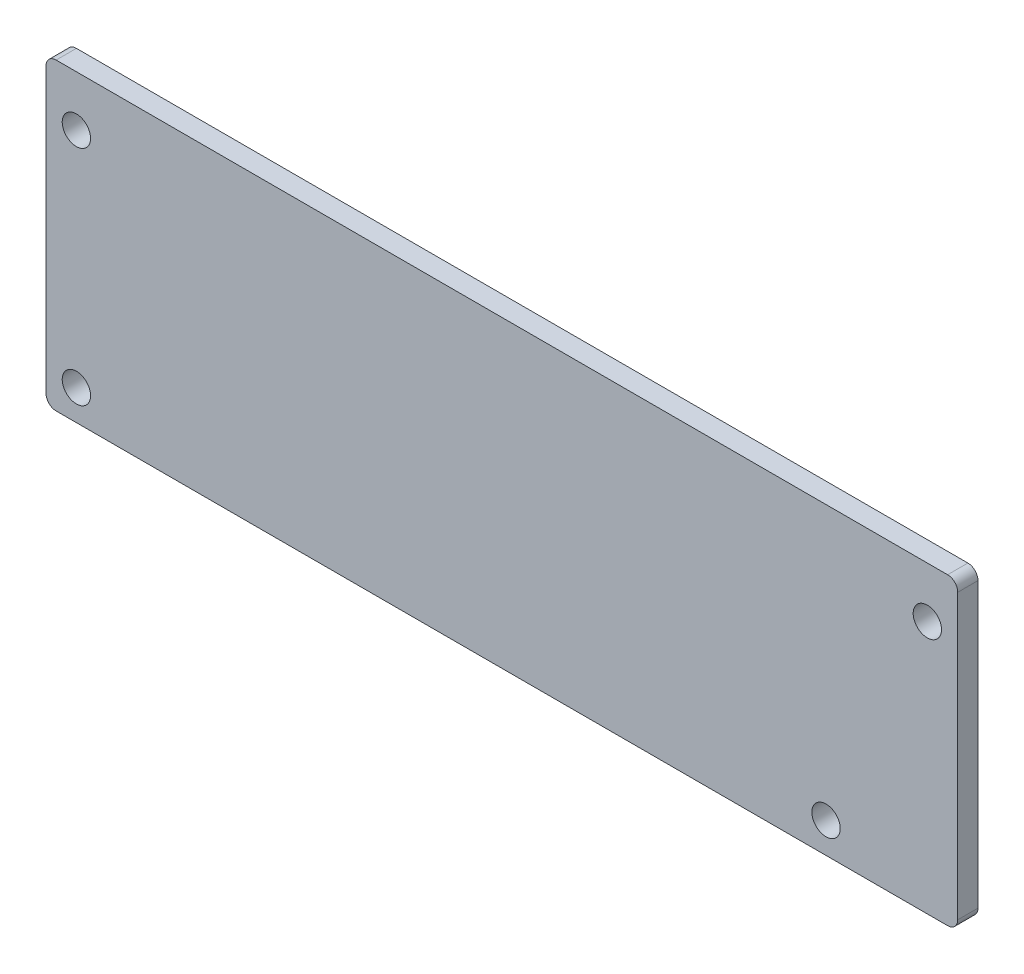
SolidWorks part; units mm, degrees
ref_plane "Front" through (0, 0, 0) normal (0, 0, 1) x (1, 0, 0)
ref_plane "Top" through (0, 0, 0) normal (0, 1, 0) x (1, 0, 0)
ref_plane "Right" through (0, 0, 0) normal (1, 0, 0) x (0, 0, -1)
sketch "Эскиз1" plane through (0, 0, 0) normal (0, 0, 1) x (1, 0, 0)
  line L0 (78, 0) -> (89, 0)
  line L1 (1, 0) -> (60.9667, 0)
  line L2 (0, 1) -> (0, 29)
  line L3 (1, 30) -> (89, 30)
  line L4 (90, 12) -> (90, 29)
  line L5 (90, 1) -> (90, 12)
  line L9 (60.9667, 0) -> (78, 0)
  circle A0 centre (3, 3) radius 1.4
  circle A1 centre (3, 25) radius 1.4
  circle A2 centre (87, 25) radius 1.4
  circle A3 centre (77, 3) radius 1.4
  arc A4 (89, 0) -> (90, 1) centre (89, 1) ccw
  arc A7 (89, 30) -> (90, 29) centre (89, 29) cw
  arc A8 (0, 29) -> (1, 30) centre (1, 29) cw
  arc A9 (1, 0) -> (0, 1) centre (1, 1) cw
  point P25 (0, 30)
  point P28 (0, 0)
  point P35 (60, 0)
  point P38 (60, -8.5)
  point P44 (30, 0)
  dimension "D5" = 2.8
  dimension "D8" = 2.8
  dimension "D10" = 2.8
  dimension "D14" = 2.8
  dimension "D13" = 1
  dimension "D15" = 1
  dimension "D2" = 25
  dimension "D3" = 3
  dimension "D4" = 3
  dimension "D6" = 3
  dimension "D7" = 22
  dimension "D9" = 3
  dimension "D11" = 13
  dimension "D12" = 3
  dimension "D16" = 30
  dimension "D17" = 90
extrude "Бобышка-Вытянуть1" add sketch "Эскиз1" along normal blind 2
sketch "Эскиз2" plane through (0, 0, 0) normal (0, 0, -1) x (-1, 0, 0)
  line L0 (-82, 28) -> (-8, 28)
  line L1 (-7, 27) -> (-7, 23)
  line L2 (-6, 22) -> (-3, 22)
  line L3 (-2, 21) -> (-2, 8)
  line L4 (-3, 7) -> (-6, 7)
  line L5 (-7, 6) -> (-7, 3)
  line L6 (-8, 2) -> (-72, 2)
  line L7 (-73, 3) -> (-73, 6)
  line L8 (-74, 7) -> (-78.5, 7)
  line L9 (-79.5, 6) -> (-79.5, 2.5)
  line L10 (-80.5, 1.5) -> (-87.5, 1.5)
  line L11 (-88.5, 2.5) -> (-88.5, 21)
  line L12 (-87.5, 22) -> (-84, 22)
  line L13 (-83, 23) -> (-83, 27)
  line L14 (-89, 30) -> (-1, 30) construction
  line L15 (0, 29) -> (0, 1) construction
  line L16 (-1, 0) -> (-89, 0) construction
  line L17 (-90, 1) -> (-90, 29) construction
  arc A0 (-87.5, 1.5) -> (-88.5, 2.5) centre (-87.5, 2.5) cw
  arc A1 (-73, 6) -> (-74, 7) centre (-74, 6) ccw
  arc A2 (-78.5, 7) -> (-79.5, 6) centre (-78.5, 6) ccw
  arc A3 (-79.5, 2.5) -> (-80.5, 1.5) centre (-80.5, 2.5) cw
  arc A4 (-7, 3) -> (-8, 2) centre (-8, 3) cw
  arc A5 (-6, 7) -> (-7, 6) centre (-6, 6) ccw
  arc A6 (-2, 8) -> (-3, 7) centre (-3, 8) cw
  arc A7 (-3, 22) -> (-2, 21) centre (-3, 21) cw
  arc A8 (-7, 23) -> (-6, 22) centre (-6, 23) ccw
  arc A9 (-8, 28) -> (-7, 27) centre (-8, 27) cw
  arc A10 (-82, 28) -> (-83, 27) centre (-82, 27) ccw
  arc A11 (-84, 22) -> (-83, 23) centre (-84, 23) ccw
  arc A12 (-88.5, 21) -> (-87.5, 22) centre (-87.5, 21) cw
  arc A13 (-72, 2) -> (-73, 3) centre (-72, 3) cw
  point P23 (-4.5, 22)
  point P28 (-73, 7)
  point P31 (-79.5, 7)
  dimension "D15" = 1
  dimension "D16" = 1
  dimension "D1" = 2
  dimension "D2" = 2
  dimension "D3" = 2
  dimension "D4" = 1.5
  dimension "D5" = 1.5
  dimension "D6" = 7
  dimension "D7" = 8
  dimension "D8" = 8
  dimension "D9" = 7
  dimension "D10" = 7
  dimension "D11" = 7
  dimension "D12" = 6.5
  dimension "D13" = 10.5
  dimension "D14" = 7
extrude "Вырез-Вытянуть1" cut sketch "Эскиз2" against normal blind 1
